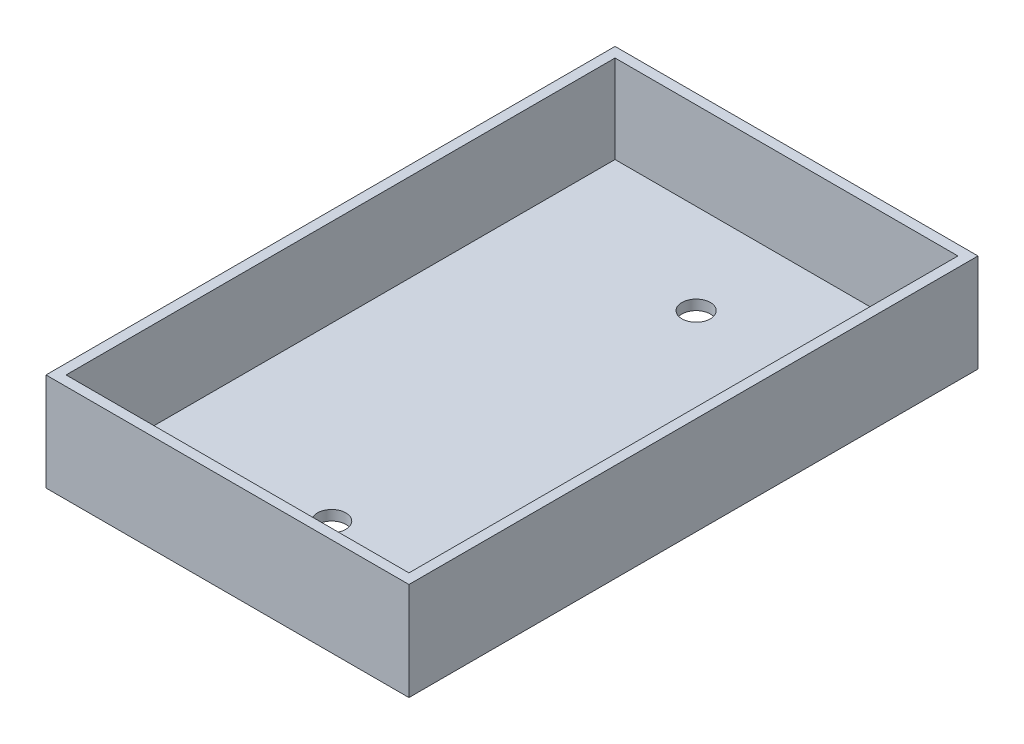
SolidWorks part; units mm, degrees
material "ABS"
ref_plane "Front Plane" through (0, 0, 0) normal (0, 0, 1) x (1, 0, 0)
ref_plane "Top Plane" through (0, 0, 0) normal (0, 1, 0) x (1, 0, 0)
ref_plane "Right Plane" through (0, 0, 0) normal (1, 0, 0) x (0, 0, -1)
sketch "Sketch1" plane through (0, 0, 0) normal (0, 1, 0) x (1, 0, 0)
  line L1 (0, 0) -> (57.404, 0)
  line L2 (0, 0) -> (0, -90)
  line L3 (0, -90) -> (57.404, -90)
  line L4 (57.404, 0) -> (57.404, -90)
  dimension "D1" = 57.404
  dimension "D2" = 90
extrude "Boss-Extrude1" add sketch "Sketch1" along normal blind 1.5875
sketch "Sketch2" plane through (57.404, 0, 0) normal (1, 0, 0) x (0, 0, -1)
  line L0 (0, 1.5875) -> (0, 0) construction
  line L1 (-90, 1.5875) -> (0, 1.5875)
  line L2 (-90, 1.5875) -> (-90, 15.494)
  line L3 (-90, 15.494) -> (0, 15.494)
  line L4 (0, 1.5875) -> (0, 15.494)
  line L5 (-90, 0) -> (0, 0) construction
  point P7 (0, 0.7937)
  dimension "D2" = 15.494
extrude "Boss-Extrude2" add sketch "Sketch2" against normal blind 1.5875
sketch "Sketch3" plane through (55.8165, 0, 0) normal (-1, 0, 0) x (0, 0, 1)
  line L0 (0, 15.494) -> (90, 15.494) construction
  line L4 (1.5875, 3.175) -> (1.5875, 1.5875)
  line L5 (90, 1.5875) -> (0, 1.5875) construction
  line L6 (88.4125, 3.175) -> (88.4125, 1.5875)
  line L8 (88.4125, 3.175) -> (88.4125, 13.9065)
  line L9 (88.4125, 13.9065) -> (1.5875, 13.9065)
  line L10 (1.5875, 13.9065) -> (1.5875, 3.175)
  line L11 (1.5875, 3.175) -> (88.4125, 3.175)
  line L12 (88.4125, 3.175) -> (88.4125, 15.494)
  line L14 (1.5875, 15.494) -> (1.5875, 3.175)
  line L15 (1.5875, 3.175) -> (88.4125, 3.175)
  dimension "D1" = 1.5875
extrude "Boss-Extrude3" add sketch "Sketch3" along normal offset from surface (54.229 mm away) 1.5875 up to face at (0, 0.7937, 45)
sketch "Sketch4" plane through (1.5875, 0, 0) normal (-1, 0, 0) x (0, 0, 1)
  line L4 (0, 0) -> (90, 0)
  line L5 (0, 15.494) -> (0, 0)
  line L6 (90, 15.494) -> (0, 15.494)
  line L7 (90, 0) -> (90, 15.494)
  line L8 (0, 0) -> (90, 0)
  line L9 (0, 15.494) -> (0, 0)
  line L10 (90, 15.494) -> (0, 15.494)
  line L11 (90, 0) -> (90, 15.494)
  dimension "D1" = 0
extrude "Boss-Extrude4" add sketch "Sketch4" along normal blind 1.5875
hole_wizard "#8 Clearance Hole1" positions "Sketch5" profile "Sketch6" hole size "#8" standard "ANSI Inch" end condition up to next
sketch "Sketch5" plane through (0, 1.5875, 0) normal (0, 1, 0) x (1, 0, 0)
  line L0 (28.702, -73.5203) -> (28.702, -15.875)
  line L10 (57.404, 0) -> (0, 0)
  line L11 (57.404, -90) -> (57.404, 0)
  line L12 (0, -90) -> (57.404, -90)
  line L14 (57.404, 0) -> (0, 0)
  line L15 (57.404, -90) -> (57.404, 0)
  line L16 (0, -90) -> (57.404, -90)
  line L17 (28.702, -15.875) -> (28.702, 0)
  line L19 (28.702, -73.5203) -> (28.702, -90)
  line L43 (0, 0) -> (0, -90)
  line L44 (0, 0) -> (0, -90)
  point P0 (28.702, -73.5203)
  point P2 (28.702, -15.875)
  point P89 (28.702, 0)
  dimension "D1" = 15.875
  dimension "D3" = 57.6453
  dimension "D2" = 0
sketch "Sketch6" plane through (28.702, 1.5875, 73.5203) normal (1, 0, 0) x (0, 0, 1)
  line L0 (0, 0) -> (0, 1.5875)
  line L1 (0, 1.5875) -> (2.2479, 1.5875)
  line L2 (2.2479, 1.5875) -> (2.2479, 0)
  line L5 (2.2479, 0) -> (0, 0)
  line L11 (0, -6.35) -> (0, 107.95) construction
  dimension "Thru Hole Dia." = 4.4958
  dimension "Thru Hole Depth" = 1.5875
sketch "Sketch8" plane through (57.404, 0, 0) normal (1, 0, 0) x (0, 0, -1)
  text T0 "FRONT"
